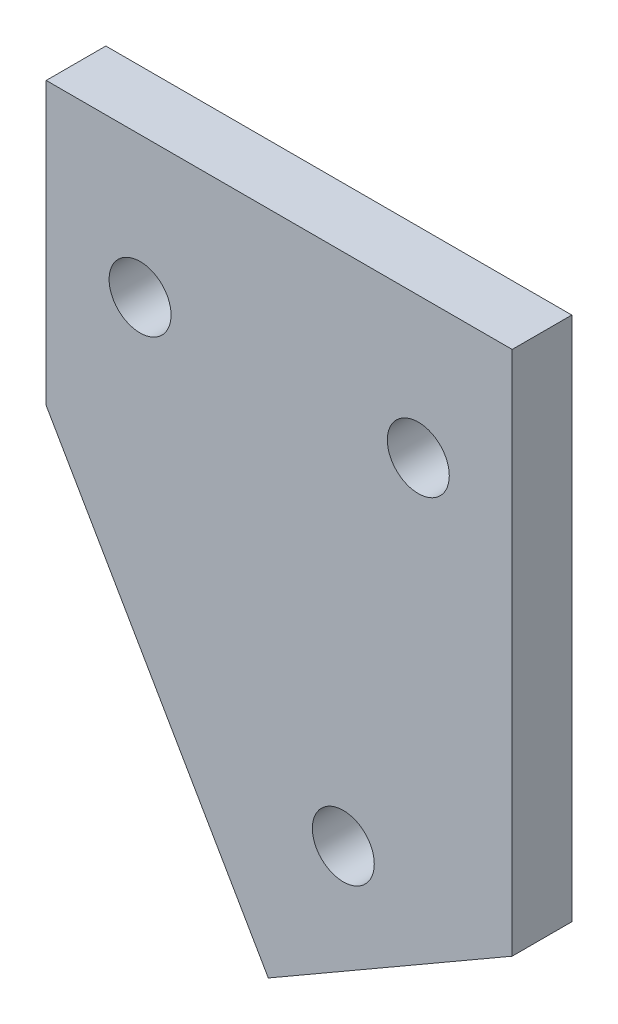
SolidWorks part; units mm, degrees
ref_plane "Front Plane" through (0, 0, 0) normal (0, 0, 1) x (1, 0, 0)
ref_plane "Top Plane" through (0, 0, 0) normal (0, 1, 0) x (1, 0, 0)
ref_plane "Right Plane" through (0, 0, 0) normal (1, 0, 0) x (0, 0, -1)
sketch "Sketch1" plane through (0, 0, 0) normal (0, 0, 1) x (1, 0, 0)
  line L0 (0, 0) -> (11.8301, -20.4904)
  line L1 (11.8301, -20.4904) -> (24.8205, -12.9904)
  line L2 (24.8205, -12.9904) -> (24.8205, 15)
  line L3 (24.8205, 15) -> (0, 15)
  line L4 (0, 15) -> (0, 0)
  line L5 (0, 0) -> (24.8205, 0) construction
  line L6 (24.8205, -12.9904) -> (17.3205, 0) construction
  line L7 (0, 7.5) -> (24.8205, 7.5) construction
  line L8 (18.3253, -16.7404) -> (15.8253, -12.4103) construction
  circle A0 centre (15.8253, -12.4103) radius 1.65
  circle A1 centre (5, 7.5) radius 1.65
  circle A2 centre (19.8205, 7.5) radius 1.65
  dimension "D3" = 3.3
  dimension "D1" = 15
  dimension "D2" = 30
  dimension "D4" = 5
  dimension "D5" = 5
  dimension "D6" = 5
  dimension "D7" = 15
extrude "Boss-Extrude1" add sketch "Sketch1" along normal blind 3.175
